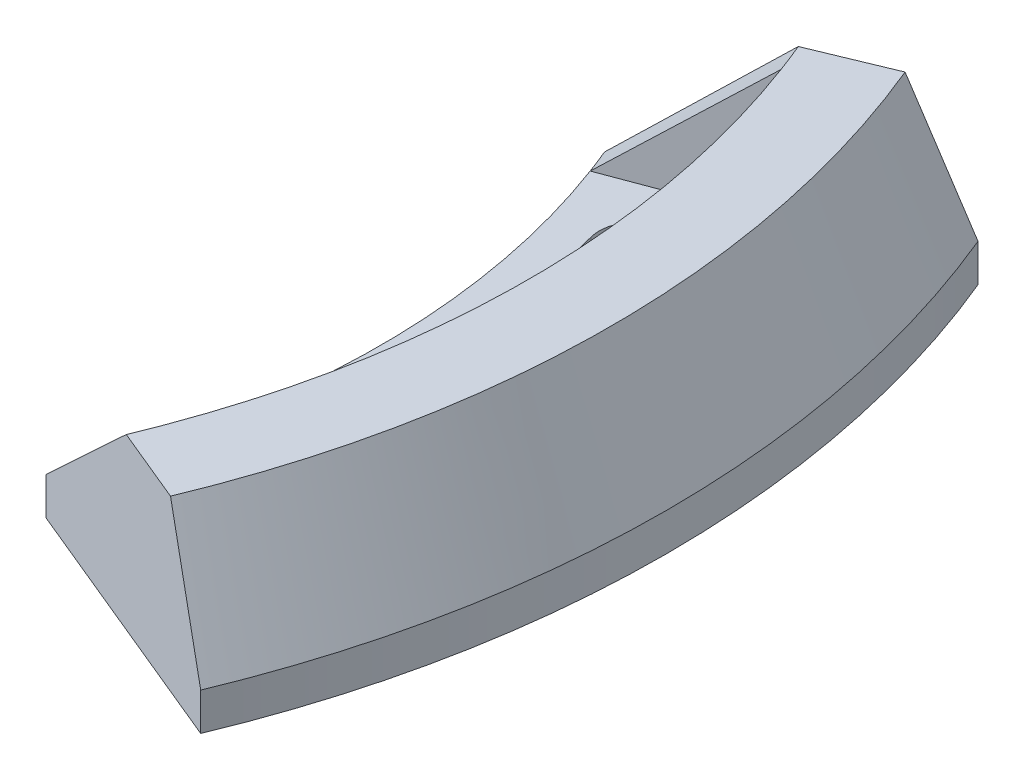
SolidWorks part; units mm, degrees
ref_plane "Front Plane" through (0, 0, 0) normal (0, 0, 1) x (1, 0, 0)
ref_plane "Top Plane" through (0, 0, 0) normal (0, 1, 0) x (1, 0, 0)
ref_plane "Right Plane" through (0, 0, 0) normal (1, 0, 0) x (0, 0, -1)
sketch "Sketch1" plane through (0, 0, 0) normal (0, 0, 1) x (1, 0, 0)
  line L0 (0, 0) -> (97, 0) construction
  line L1 (97, 0) -> (97, 5)
  line L2 (97, 5) -> (124.1364, 5)
  line L3 (124.1364, 5) -> (116.7175, 22.4778)
  line L4 (116.7175, 22.4778) -> (127.5811, 22.4778)
  line L5 (127.5811, 22.4778) -> (135, 5)
  line L6 (135, 5) -> (135, 0)
  line L7 (135, 0) -> (97, 0)
  line L8 (123.2924, 6.9882) -> (118.6899, 5.0346) construction
  line L9 (123.2924, 6.9882) -> (115.8685, 24.4778) construction
  line L10 (115.8685, 24.4778) -> (111.266, 22.5242) construction
  line L11 (111.266, 22.5242) -> (109.9303, 19.7845) construction
  line L12 (109.9303, 19.7845) -> (102.5663, 16.6586) construction
  line L13 (102.5663, 16.6586) -> (105.6921, 9.2946) construction
  line L14 (111.7838, 5.9221) -> (115.8685, 24.4778) construction
  line L15 (0, 0) -> (0, 47.9771) construction
  arc A0 (118.6899, 5.0346) -> (105.6921, 9.2946) centre (117.558, 23.5398) cw construction
  dimension "D1" = 15.3
  dimension "D2" = 19
  dimension "D3" = 5
  dimension "D4" = 2
  dimension "D5" = 8
  dimension "D6" = 19
  dimension "D7" = 8
  dimension "D8" = 5
  dimension "D9" = 38
  dimension "67" = 67
  dimension "D10" = 2
  dimension "D11" = 10
  dimension "D12" = 135
  dimension "D13" = 5
revolve "Revolve1" add sketch "Sketch1" angle 45 mid plane about L15
sketch "Sketch2" plane through (0, 0, 0) normal (-0.3827, 0, 0.9239) x (0.9239, 0, 0.3827)
  line L0 (97, 5) -> (116.7175, 22.4778)
  line L1 (116.7175, 22.4778) -> (124.1364, 5)
  line L2 (124.1364, 5) -> (97, 5)
  line L3 (0, 0) -> (0, 31.8493) construction
revolve "Revolve2" add sketch "Sketch2" angle 2 about L3
mirror "Mirror1" about plane through (0, 0, 0) normal (0, 0, 1) of "Revolve2"
sketch "Sketch3" plane through (0, 5, 0) normal (0, 1, 0) x (1, 0, 0)
  line L0 (103.3541, 27.6936) -> (0, 0) construction
  line L1 (0, 0) -> (103.3541, -27.6936) construction
  line L2 (0, 0) -> (107, 0) construction
  arc A0 (124.7237, -51.6623) -> (124.7237, 51.6623) centre (0, 0) ccw construction
  arc A1 (103.3541, -27.6936) -> (103.3541, 27.6936) centre (0, 0) ccw construction
  arc A2 (108.1837, -28.9877) -> (108.1837, 28.9877) centre (0, 0) ccw
  arc A3 (98.5244, -26.3995) -> (98.5244, 26.3995) centre (0, 0) ccw
  arc A4 (98.5244, -26.3995) -> (108.1837, -28.9877) centre (103.3541, -27.6936) ccw
  arc A5 (108.1837, 28.9877) -> (98.5244, 26.3995) centre (103.3541, 27.6936) ccw
  point P8 (107, 0)
  dimension "D1" = 28
  dimension "D2" = 10
  dimension "D3" = 15
  dimension "D4" = 15
extrude "Cut-Extrude1" cut sketch "Sketch3" against normal through all separate body contours A3 A5 A2 A4
equation "\"D4@Sketch3\"=\"D3@Sketch3\""
